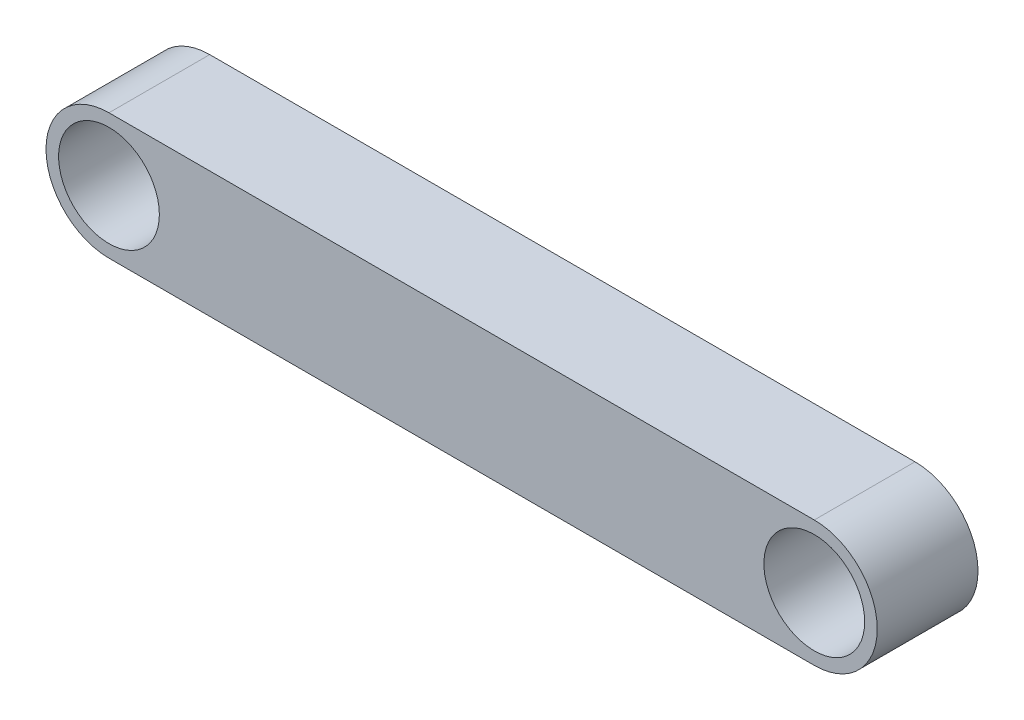
SolidWorks part; units mm, degrees
ref_plane "Front Plane" through (0, 0, 0) normal (0, 0, 1) x (1, 0, 0)
ref_plane "Top Plane" through (0, 0, 0) normal (0, 1, 0) x (1, 0, 0)
ref_plane "Right Plane" through (0, 0, 0) normal (1, 0, 0) x (0, 0, -1)
sketch "Sketch3" plane through (0, 0, 0) normal (0, 0, 1) x (1, 0, 0)
  line L0 (0, 0) -> (140, 0) construction
  line L1 (0, 12.5) -> (140, 12.5)
  line L2 (0, -12.5) -> (140, -12.5)
  arc A0 (0, 12.5) -> (0, -12.5) centre (0, 0) ccw
  arc A1 (140, -12.5) -> (140, 12.5) centre (140, 0) ccw
  circle A2 centre (0, 0) radius 10
  circle A3 centre (140, 0) radius 10
  point P2 (70, 0)
  point P11 (0, 0)
  point P12 (0, 0)
  point P14 (0, 0)
  dimension "D1" = 20
  dimension "D2" = 20
  dimension "D3" = 25
  dimension "D4" = 140
extrude "Boss-Extrude2" add sketch "Sketch3" along normal mid plane 20
